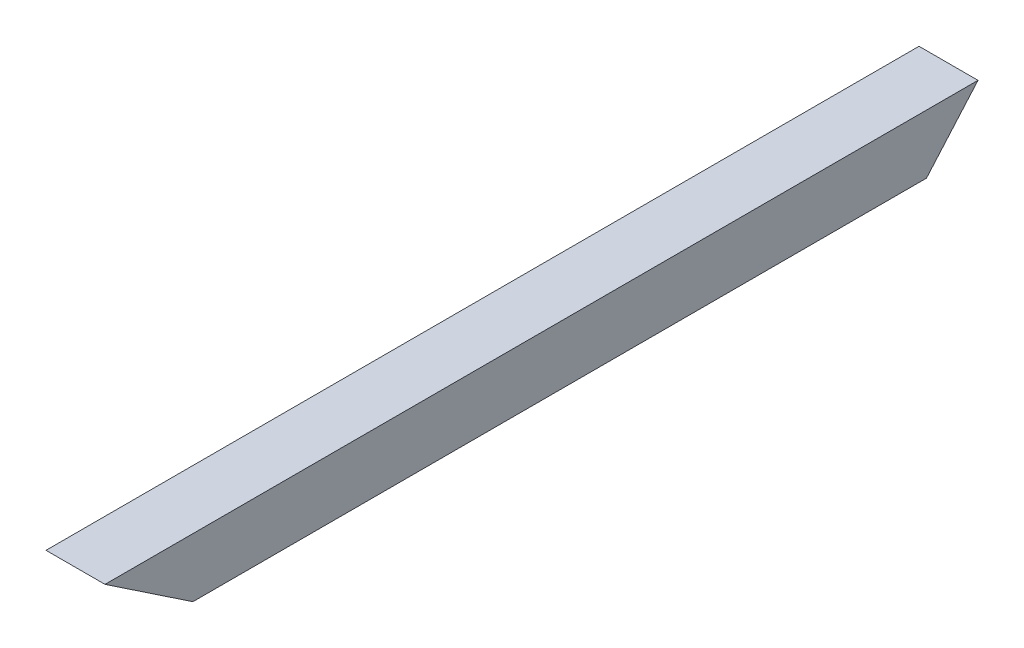
SolidWorks part; units mm, degrees
ref_plane "Front Plane" through (0, 0, 0) normal (0, 0, 1) x (1, 0, 0)
ref_plane "Top Plane" through (0, 0, 0) normal (0, 1, 0) x (1, 0, 0)
ref_plane "Right Plane" through (0, 0, 0) normal (1, 0, 0) x (0, 0, -1)
sketch "Sketch1" plane through (0, 0, 0) normal (0, 0, 1) x (1, 0, 0)
  line L1 (11.049, 11.049) -> (-11.049, 11.049)
  line L2 (11.049, 11.049) -> (11.049, -11.049)
  line L3 (11.049, -11.049) -> (-11.049, -11.049)
  line L4 (-11.049, 11.049) -> (-11.049, -11.049)
  line L5 (11.049, 11.049) -> (-11.049, -11.049) construction
  line L6 (11.049, -11.049) -> (-11.049, 11.049) construction
  line L7 (12.7, 12.7) -> (-12.7, 12.7)
  line L8 (12.7, 12.7) -> (12.7, -12.7)
  line L9 (12.7, -12.7) -> (-12.7, -12.7)
  line L10 (-12.7, 12.7) -> (-12.7, -12.7)
  line L11 (12.7, 12.7) -> (-12.7, -12.7) construction
  line L12 (12.7, -12.7) -> (-12.7, 12.7) construction
  point P0 (0, 0)
  point P6 (0, 0)
  dimension "D3" = 1.651
  dimension "D4" = 1.651
  dimension "D5" = 1.651
  dimension "D2" = 25.4
  dimension "D1" = 25.4
extrude "Boss-Extrude1" add sketch "Sketch1" along normal up to vertex (378.3092 mm away)
sketch "Sketch3" plane through (0, 0, 0) normal (0, 1, 0) x (1, 0, 0)
  line L0 (0, 12.8662) -> (0, -262.1311) construction
  line L1 (0, -13.97) -> (0, 13.97) construction
ref_point "Point1"
sketch "Sketch4" plane through (-12.7, 0, 0) normal (-1, 0, 0) x (0, 0, 1)
  line L0 (0, 12.7) -> (22.2316, -12.7491)
  line L1 (22.2316, -12.7491) -> (0, -16.3911)
  line L2 (0, -16.3911) -> (0, 12.7)
  dimension "D1" = 41.14
extrude "Cut-Extrude2" cut sketch "Sketch4" against normal through all
ref_plane "Plane1" through (0, -132.2171, 182.7669) normal (0, 0.5572, 0.8304) x (1, 0, 0)
sketch "Sketch5" plane through (0, -132.2171, 182.7669) normal (0, 0.5572, 0.8304) x (1, 0, 0)
  line L1 (-12.7, 12.7) -> (12.7, 12.7)
  line L2 (-12.7, 12.7) -> (-12.7, -12.7)
  line L3 (-12.7, -12.7) -> (12.7, -12.7)
  line L4 (12.7, 12.7) -> (12.7, -12.7)
  line L5 (-12.7, 12.7) -> (12.7, -12.7) construction
  line L6 (-12.7, -12.7) -> (12.7, 12.7) construction
  point P0 (0, 0)
  dimension "D1" = 25.4
  dimension "D2" = 25.4
extrude "Cut-Extrude3" cut sketch "Sketch5" along normal through all
equation "\"c1c2Len\"= 250"
equation "\"D1\"= \"c1c2Len\""
equation "\"1inchSquareTubeLen\"=25.4"
equation "\"D2@Sketch1\"=\"1inchSquareTubeLen\""
equation "\"D1@Sketch1\"=\"1inchSquareTubeLen\""
equation "\"squareTubeWallThickness\"=1.651"
equation "\"D5@Sketch1\"=\"squareTubeWallThickness\""
equation "\"D4@Sketch1\"=\"squareTubeWallThickness\""
equation "\"D3@Sketch1\"=\"squareTubeWallThickness\""
equation "\"D1@Sketch4\"=90-arccos(250/380)"
